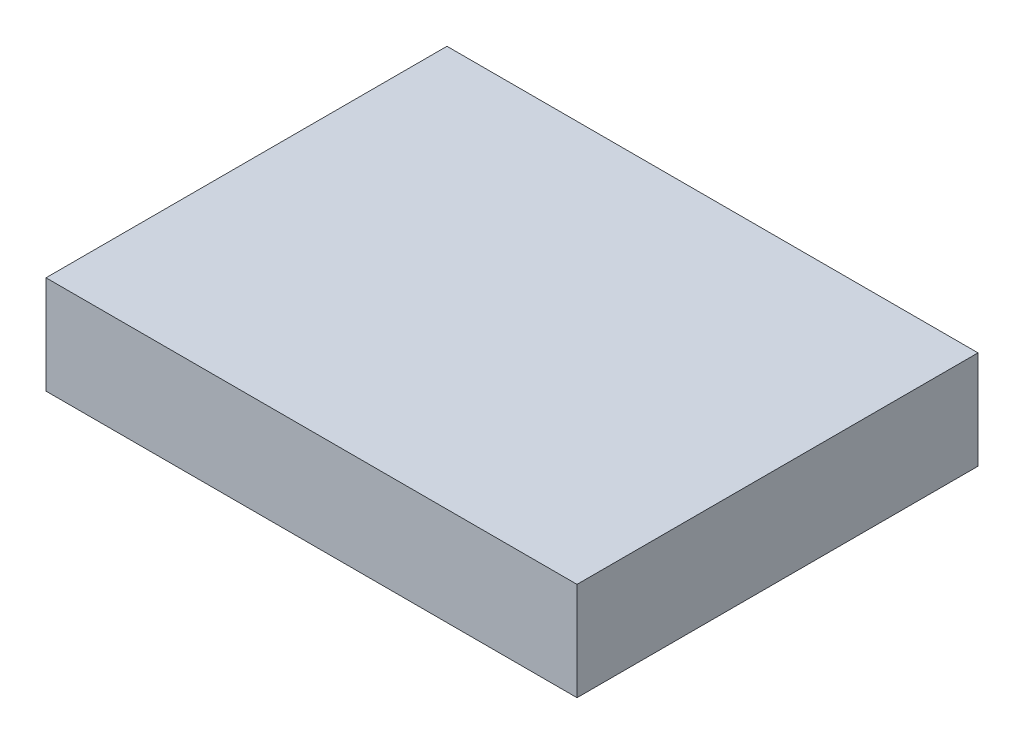
SolidWorks part; units mm, degrees
ref_plane "Front Plane" through (0, 0, 0) normal (0, 0, 1) x (1, 0, 0)
ref_plane "Top Plane" through (0, 0, 0) normal (0, 1, 0) x (1, 0, 0)
ref_plane "Right Plane" through (0, 0, 0) normal (1, 0, 0) x (0, 0, -1)
sketch "Sketch1" plane through (0, 0, 0) normal (0, 1, 0) x (1, 0, 0)
  line L1 (0, 0) -> (49, 0)
  line L2 (0, 0) -> (0, 37)
  line L3 (0, 37) -> (49, 37)
  line L4 (49, 0) -> (49, 37)
  dimension "D1" = 49
  dimension "D2" = 37
extrude "Boss-Extrude1" add sketch "Sketch1" along normal blind 9.06
